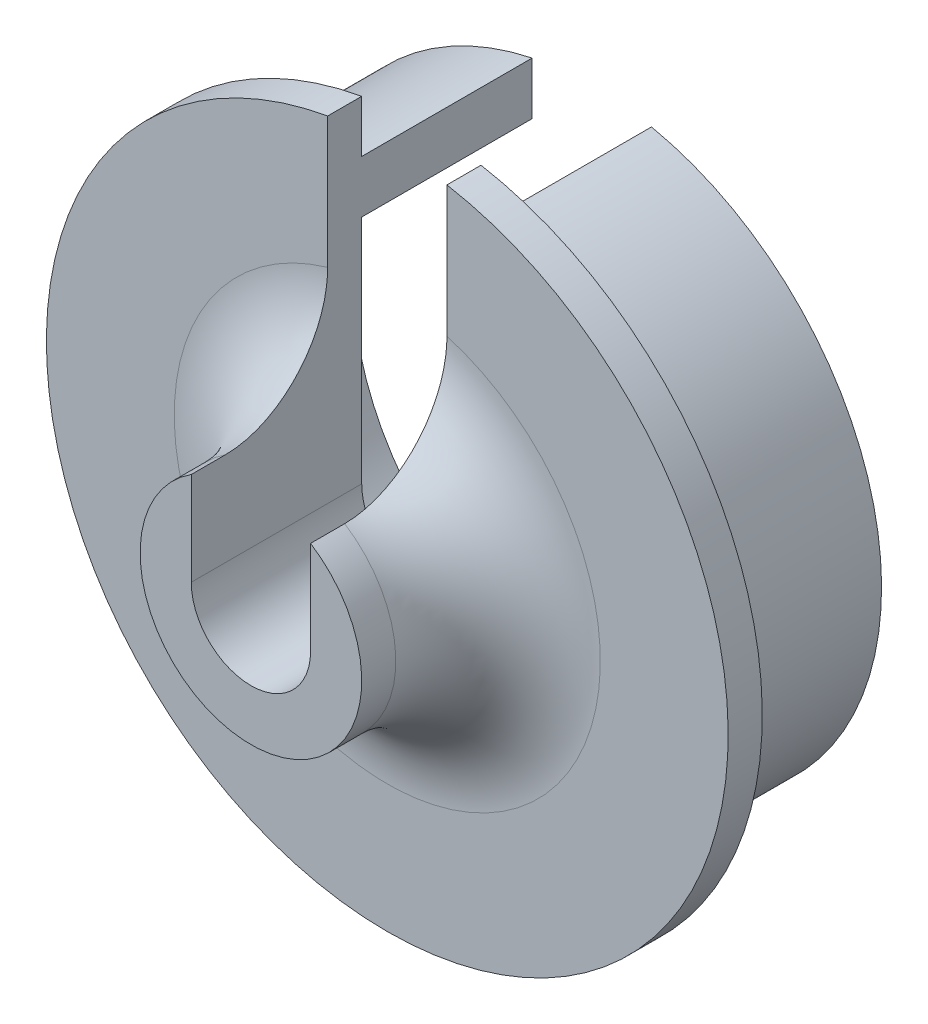
SolidWorks part; units mm, degrees
material "ABS"
ref_plane "Front Plane" through (0, 0, 0) normal (0, 0, 1) x (1, 0, 0)
ref_plane "Top Plane" through (0, 0, 0) normal (0, 1, 0) x (1, 0, 0)
ref_plane "Right Plane" through (0, 0, 0) normal (1, 0, 0) x (0, 0, -1)
sketch "Sketch1" plane through (0, 0, 0) normal (1, 0, 0) x (0, 0, -1)
  line L0 (0, 0) -> (10, 0) construction
  line L1 (0, 1.75) -> (0, 3.25)
  line L2 (0, 3.25) -> (1, 3.25)
  line L3 (4, 6.25) -> (4, 10)
  line L4 (4, 10) -> (5, 10)
  line L5 (5, 10) -> (5, 8.5)
  line L6 (5, 8.5) -> (10, 8.5)
  line L7 (10, 8.5) -> (10, 7)
  line L8 (10, 7) -> (5, 7)
  line L9 (5, 7) -> (5, 1.75)
  line L10 (5, 1.75) -> (0, 1.75)
  arc A0 (1, 3.25) -> (4, 6.25) centre (1, 6.25) ccw
  dimension "D11" = 3
  dimension "D1" = 10
  dimension "D2" = 1.75
  dimension "D3" = 1.5
  dimension "D4" = 1
  dimension "D5" = 1.5
  dimension "D6" = 5
  dimension "D7" = 5
  dimension "D8" = 7
  dimension "D9" = 10
  dimension "D10" = 4
revolve "Revolve1" add sketch "Sketch1" angle 360 about L0
sketch "Sketch2" plane through (0, 0, -5) normal (0, 0, -1) x (-1, 0, 0)
  line L0 (-1.75, 0) -> (-1.75, 9.8457)
  line L1 (1.75, 0) -> (1.75, 9.8457)
  circle A1 centre (0, 0) radius 10 construction
  circle A2 centre (0, 0) radius 1.75
  circle A3 centre (0, 0) radius 1.75
  circle A6 centre (0, 0) radius 10
  circle A7 centre (0, 0) radius 10
  circle M3 centre (0, 0) radius 7
  circle M4 centre (0, 0) radius 1.75
  dimension "D1" = 0
  dimension "D2" = 0
extrude "Cut-Extrude1" cut sketch "Sketch2" against normal through all both and the other way through all contours L1 A7 L0 M3 | L1 L0 M4 M3
